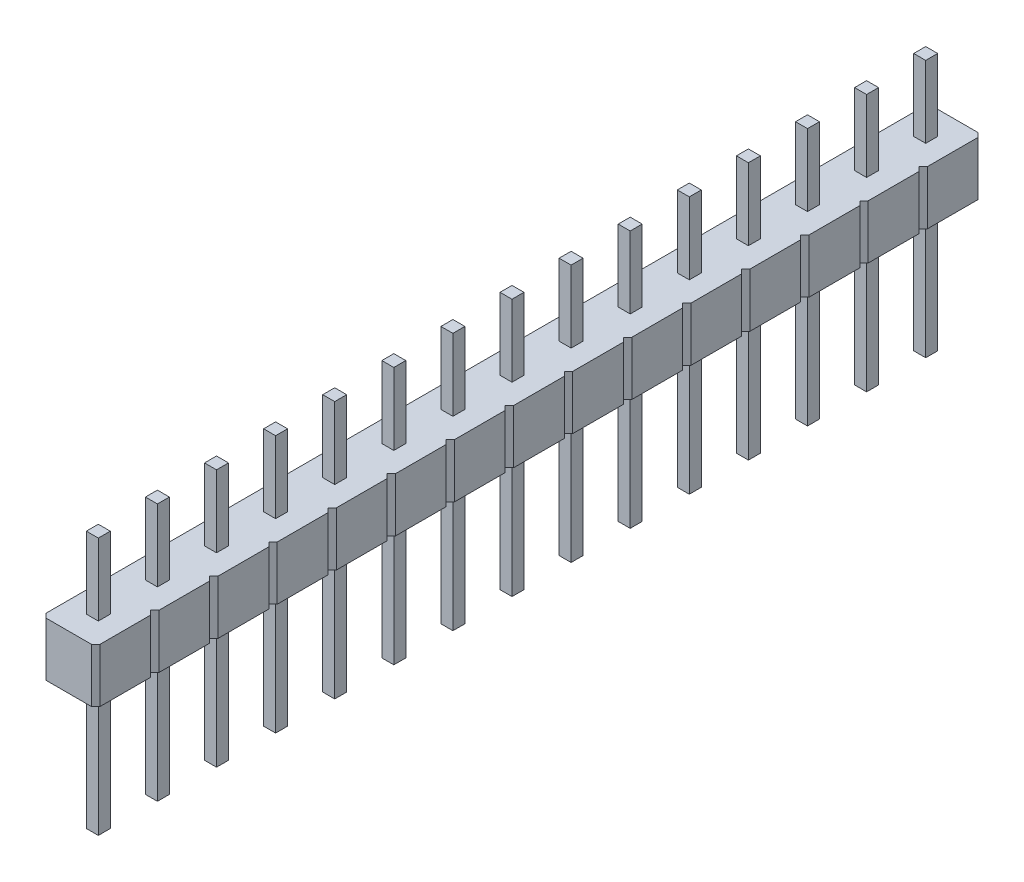
SolidWorks part; units mm, degrees
ref_plane "Front" through (0, 0, 0) normal (0, 0, 1) x (1, 0, 0)
ref_plane "Top" through (0, 0, 0) normal (0, 1, 0) x (1, 0, 0)
ref_plane "Right" through (0, 0, 0) normal (1, 0, 0) x (0, 0, -1)
sketch "Sketch1" plane through (0, 0, 0) normal (0, 1, 0) x (1, 0, 0)
  line L1 (-1.143, 18.796) -> (1.143, 18.796)
  line L2 (-1.143, 18.796) -> (-1.143, -18.796)
  line L3 (-1.143, -18.796) -> (1.143, -18.796)
  line L4 (1.143, 18.796) -> (1.143, -18.796)
  line L5 (-1.143, 18.796) -> (1.143, -18.796) construction
  line L6 (-1.143, -18.796) -> (1.143, 18.796) construction
  point P0 (0, 0)
  dimension "D1" = 37.592
  dimension "D2" = 2.286
extrude "Boss-Extrude1" add sketch "Sketch1" along normal blind 2.286
sketch "Sketch2" plane through (0, 2.286, 0) normal (0, 1, 0) x (1, 0, 0)
  line L0 (1.143, 18.796) -> (-1.143, 18.796) construction
  line L1 (-0.254, 17.797) -> (0.254, 17.797)
  line L2 (-0.254, 17.797) -> (-0.254, 17.289)
  line L3 (-0.254, 17.289) -> (0.254, 17.289)
  line L4 (0.254, 17.797) -> (0.254, 17.289)
  line L5 (-0.254, 17.797) -> (0.254, 17.289) construction
  line L6 (-0.254, 17.289) -> (0.254, 17.797) construction
  point P0 (0, 17.543)
  dimension "D1" = 0.508
  dimension "D2" = 1.253
sketch "Sketch3" plane through (0, 2.286, 0) normal (0, 1, 0) x (1, 0, 0)
  line L0 (-1.143, 18.796) -> (-1.143, -18.796) construction
  line L1 (-1.143, 16.2899) -> (1.143, 16.2899)
  line L2 (-1.143, 16.2899) -> (-1.143, -18.796)
  line L3 (-1.143, -18.796) -> (1.143, -18.796)
  line L4 (1.143, 16.2899) -> (1.143, -18.796)
  line L5 (1.143, 18.796) -> (-1.143, 18.796) construction
  dimension "D1" = 2.5061
extrude "Cut-Extrude1" cut sketch "Sketch3" against normal through all
chamfer "Chamfer1" distance 0.1778 angle 45 4 edges at (-1.143, 1.143, -18.796) (1.143, 1.143, -18.796) (-1.143, 1.143, -16.2899) (1.143, 1.143, -16.2899)
extrude "Boss-Extrude2" add sketch "Sketch2" along normal blind 3.048 and the other way blind 7.874
sketch "Sketch4" plane through (0, 0, 0) normal (0, 1, 0) x (1, 0, 0)
  line L0 (0, 16.2899) -> (0, 8.1584)
  line L1 (0.9652, 16.2899) -> (-0.9652, 16.2899) construction
pattern_linear "LPattern1" count 15 spacing 2.5061 along (0, 0, 1) of bodies 103
combine bodies "Combine1" operation type add bodies to combine 115 108 113 106 111 116 104 109 114 107 112 117 105 103 110
